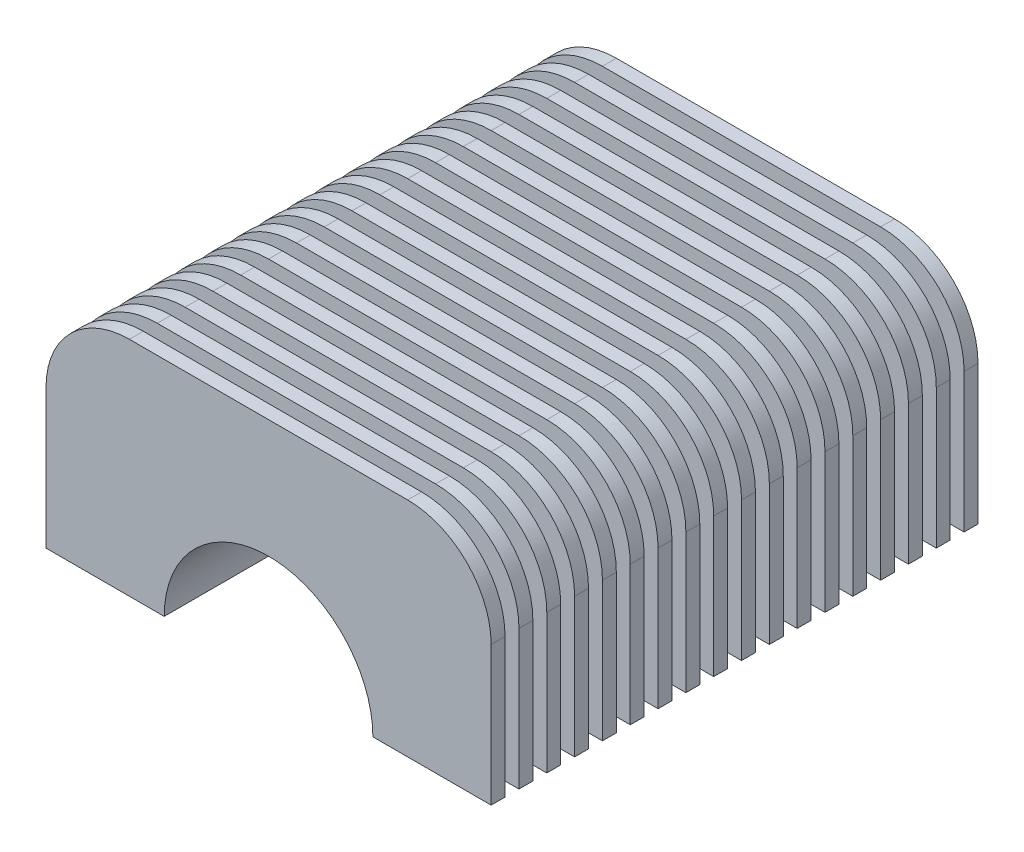
SolidWorks part; units mm, degrees
ref_plane "Płaszczyzna przednia" through (0, 0, 0) normal (0, 0, 1) x (1, 0, 0)
ref_plane "Płaszczyzna górna" through (0, 0, 0) normal (0, 1, 0) x (1, 0, 0)
ref_plane "Płaszczyzna prawa" through (0, 0, 0) normal (1, 0, 0) x (0, 0, -1)
sketch "Szkic1" plane through (0, 0, 0) normal (0, 0, 1) x (1, 0, 0)
  line L5 (62.5, 0) -> (80, 0)
  line L6 (0, 0) -> (17.5, 0)
  line L7 (0, 0) -> (0, 40)
  line L8 (0, 40) -> (80, 40)
  line L9 (80, 0) -> (80, 40)
  arc A1 (62.5, 0) -> (17.5, 0) centre (40, 0) ccw
  dimension "D3" = 17.5
  dimension "D4" = 22.5
  dimension "D1" = 40
  dimension "D2" = 80
extrude "Dodanie-wyciągnięcie1" add sketch "Szkic1" along normal blind 108
fillet "Zaokrąglenie3" radius 10 1 edges at (80, 40, 54)
fillet "Zaokrąglenie4" radius 10 1 edges at (0, 40, 54)
sketch "Szkic3" plane through (0, 0, 108) normal (0, 0, 1) x (1, 0, 0)
  line L0 (0, 0) -> (-8, 0)
  line L1 (80, 0) -> (88, 0)
  line L2 (0, 30) -> (0, 0) construction
  line L3 (70, 40) -> (10, 40) construction
  line L4 (80, 0) -> (80, 30) construction
  line L5 (0, 30) -> (0, 0)
  line L6 (70, 40) -> (10, 40)
  line L7 (80, 0) -> (80, 30)
  line L8 (88, 8) -> (88, 8)
  line L9 (88, 8) -> (88, 30)
  line L10 (70, 48) -> (10, 48)
  line L11 (-8, 30) -> (-8, 8)
  line L12 (-8, 8) -> (-8, 8)
  line L13 (-8, 0) -> (-8, 8)
  line L14 (88, 0) -> (88, 8)
  arc A0 (10, 40) -> (0, 30) centre (10, 30) ccw construction
  arc A1 (80, 30) -> (70, 40) centre (70, 30) ccw construction
  arc A2 (10, 40) -> (0, 30) centre (10, 30) ccw
  arc A3 (80, 30) -> (70, 40) centre (70, 30) ccw
  arc A4 (88, 30) -> (70, 48) centre (70, 30) ccw
  arc A5 (10, 48) -> (-8, 30) centre (10, 30) ccw
  line M2 (70, 40) -> (10, 40)
  arc M3 (10, 40) -> (0, 30) centre (10, 30) ccw
  line M4 (0, 30) -> (0, 0)
  line M8 (80, 0) -> (80, 30)
  arc M9 (80, 30) -> (70, 40) centre (70, 30) ccw
  dimension "D1" = 8
  dimension "D2" = 8
  dimension "D3" = 8
extrude "Dodanie-wyciągnięcie2" add sketch "Szkic3" against normal blind 3 contours L10 A5 L11 L13 L0 L1 L14 L9 A4 M4 M3 M2 M9 M8
pattern_linear "Szyk liniowy1" count 18 spacing 6 along (0, 0, -1) of "Dodanie-wyciągnięcie2"
